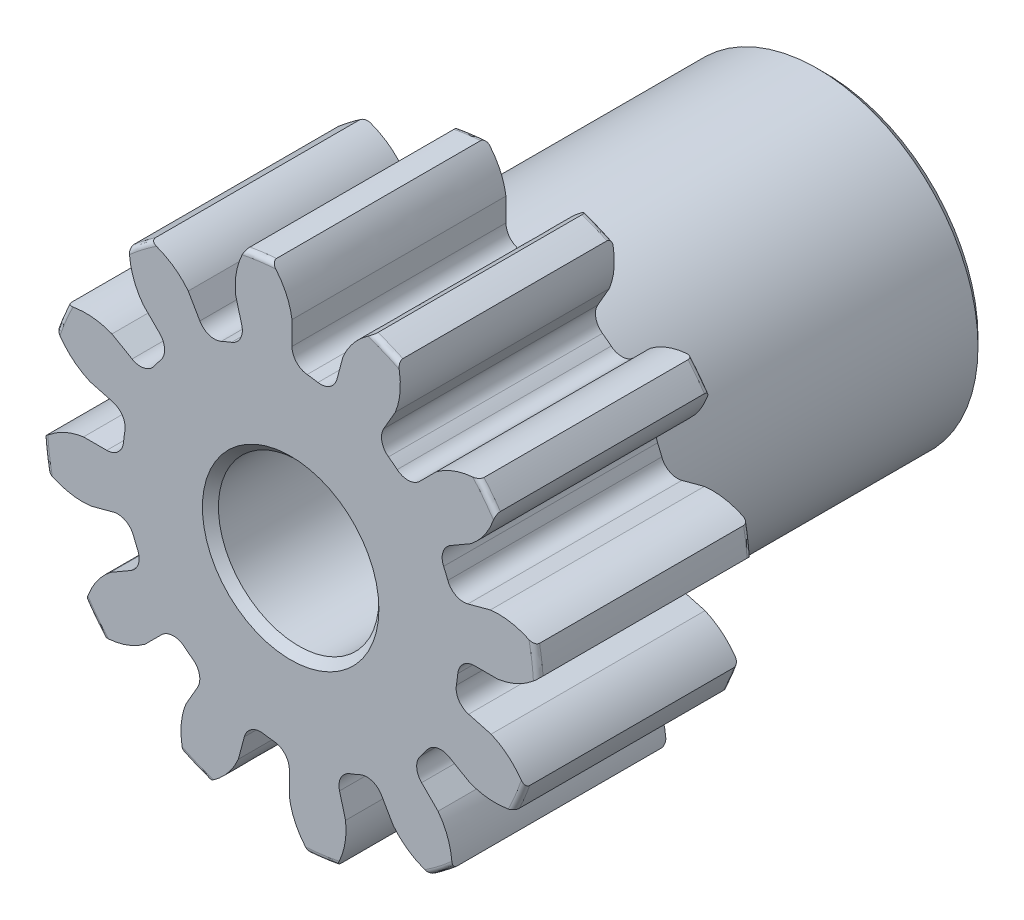
SolidWorks part; units mm, degrees
ref_plane "Front" through (0, 0, 0) normal (0, 0, 1) x (1, 0, 0)
ref_plane "Top" through (0, 0, 0) normal (0, 1, 0) x (1, 0, 0)
ref_plane "Right" through (0, 0, 0) normal (1, 0, 0) x (0, 0, -1)
sketch "Sketch1" plane through (0, 0, 0) normal (0, 0, 1) x (1, 0, 0)
  line L0 (-152.4, 0) -> (152.4, 0) construction
  circle A0 centre (0, 0) radius 3.683
  circle A1 centre (0, 0) radius 3.175 construction
  circle A3 centre (0, 0) radius 2.4924 construction
  dimension "D1" = 1.1906
  dimension "OD" = 7.366
  dimension "Ptich Dia" = 6.35
  dimension "Root Dia" = 4.9848
  dimension "D3" = 0.508
  dimension "Number of Teeth" = 304.8
extrude "Boss-Extrude1" add sketch "Sketch1" against normal blind 3.175
sketch "Sketch2" plane through (0, 0, 0) normal (1, 0, 0) x (0, 0, -1)
  line L0 (3.175, 0) -> (7.9375, 0)
  line L1 (3.175, 0) -> (3.175, 2.3812)
  line L2 (3.175, 2.3812) -> (7.9375, 2.3812)
  line L3 (7.9375, 2.3812) -> (7.9375, 0)
  point P5 (7.9375, -2.3812)
  point P6 (0, -3.683)
  point P7 (3.175, -3.683)
  point P9 (0, 3.683)
  dimension "Face Wd" = 3.175
  dimension "B Hub Dia" = 4.7625
  dimension "D O'all Lg." = 7.9375
revolve "Revolve1" add sketch "Sketch2" angle 360 about L0
fillet "Fillet2" radius 0.0737 3 edges at (3.683, 0, -3.175) (3.683, 0, 0) (2.3812, 0, -3.175)
sketch "Sketch3" plane through (0, 0, 0) normal (0, 0, 1) x (1, 0, 0)
  line L0 (0, 0) -> (0, 3.683) construction
  line L1 (-0.7696, 2.976) -> (0, 3.175)
  line L2 (-9.5921, 3.175) -> (9.5921, 3.175) construction
  line L3 (-9.2865, 0.7733) -> (9.2865, 5.5767) construction
  line L4 (-0.7696, 2.976) -> (0, 0) construction
  line L5 (-1.9631, 2.3654) -> (0, 0) construction
  line L6 (-1.9631, 2.3654) -> (-0.331, 3.7199) construction
  line L7 (-0.5367, 3.0267) -> (0, 0) construction
  line L8 (-0.5367, 3.0267) -> (0.0113, 3.1238) construction
  arc A0 (-0.7696, 2.976) -> (-1.9631, 2.3654) centre (0, 0) ccw
  circle A1 centre (0, 0) radius 3.175 construction
  circle A2 centre (0, 0) radius 3.0739 construction
  arc A3 (-0.7696, 2.976) -> (-0.5367, 3.0267) centre (0, 0) cw
  circle A4 centre (0, 0) radius 3.683 construction
  point P6 (0, 3.175)
  dimension "D1" = 0.795
  dimension "Pressure Angle" = 14.5
  dimension "D2" = 1.3514
  dimension "D3" = 2.121
  dimension "D4" = 0.2385
  dimension "D5" = 0.5565
sketch "Sketch4" plane through (0, 0, 0) normal (0, 0, 1) x (1, 0, 0)
  line L0 (0, 0) -> (0.4109, 3.1209) construction
  line L1 (0.0197, 3.0738) -> (0.0197, 2.4923)
  line L2 (0, 3.175) -> (0.8218, 3.0668) construction
  line L3 (0.7765, 2.9742) -> (0.626, 2.4125)
  line L4 (0.0197, 2.4923) -> (0, 0) construction
  line L5 (0, 0) -> (0, 3.683) construction
  line L6 (-1.9631, 2.3654) -> (-0.331, 3.7199) construction
  line L7 (-1.9631, 2.3654) -> (-0.331, 3.7199) construction
  arc A0 (0.626, 2.4125) -> (0.0197, 2.4923) centre (0, 0) ccw
  arc A1 (0, 3.175) -> (0.8218, 3.0668) centre (0, 0) cw construction
  circle A2 centre (0, 0) radius 3.175 construction
  circle A3 centre (0, 0) radius 3.0739 construction
  circle A4 centre (0, 0) radius 2.4924 construction
  arc A5 (1.2825, 3.5075) -> (-0.331, 3.7199) centre (0, 0) ccw
  spline S0 degree 2 poles (-0.331, 3.7199) (-0.0334, 3.4407) (0.0197, 3.0738) knots 0 0 0 1 1 1
  spline S1 degree 2 poles (1.2825, 3.5075) (0.9228, 3.3148) (0.7765, 2.9742) knots 0 0 0 1 1 1
  dimension "D1" = 0.8312
extrude "Cut-Extrude1" cut sketch "Sketch4" against normal through all
fillet "Fillet1" radius 0.2494 2 edges at (0.626, 2.4125, -1.5875) (0.0197, 2.4923, -1.5875)
pattern_circular "CirPattern1" count 12 over 360 about axis through (0, 0, -3.175) along (0, 0, 1) of "Cut-Extrude1", "Fillet1"
sketch "Sketch5" plane through (0, 0, 0) normal (0, 0, 1) x (1, 0, 0)
  circle A0 centre (0, 0) radius 1.1906
  circle A1 centre (0, 0) radius 1.5875 construction
  dimension "Bore Min" = 2.3813
  dimension "Bore Max" = 3.175
extrude "Cut-Extrude2" cut sketch "Sketch5" against normal through all
chamfer "Chamfer1" distance 0.1191 angle 45 3 edges at (2.3812, 0, -7.9375) (1.1906, 0, 0) (1.1906, 0, -7.9375)
sketch "Pitch Dia" plane through (0, 0, 0) normal (0, 0, 1) x (1, 0, 0)
  circle A0 centre (0, 0) radius 3.175 construction
  circle A1 centre (0, 0) radius 3.175 construction
equation "\"D1@Boss-Extrude1\" = \"Face Wd@Sketch2\""
equation "\"D2@Sketch3\" = \"D1@Sketch3\"*1.7"
equation "\"D3@Sketch3\" = \"D1@Sketch3\"+\"D2@Sketch3\"-.001"
equation "\"D4@Sketch3\" = \"D1@Sketch3\"*.3"
equation "\"D5@Sketch3\" = \"D1@Sketch3\"-\"D4@Sketch3\""
equation "\"D1@Sketch4\" = 1.5708/(\"Number of Teeth@Sketch1\"/\"Ptich Dia@Sketch1\")"
equation "\"D1@Chamfer1\" = \"B Hub Dia@Sketch2\"*.025"
equation "\"D1@CirPattern1\" = \"Number of Teeth@Sketch1\""
equation "\"D1@Fillet1\" = \"D1@Sketch4\"*.3"
equation "\"D1@Fillet2\" = \"OD@Sketch1\"*.01"
equation "\"D1@Sketch1\" = 2.250/(\"Number of Teeth@Sketch1\"/\"Ptich Dia@Sketch1\")"
